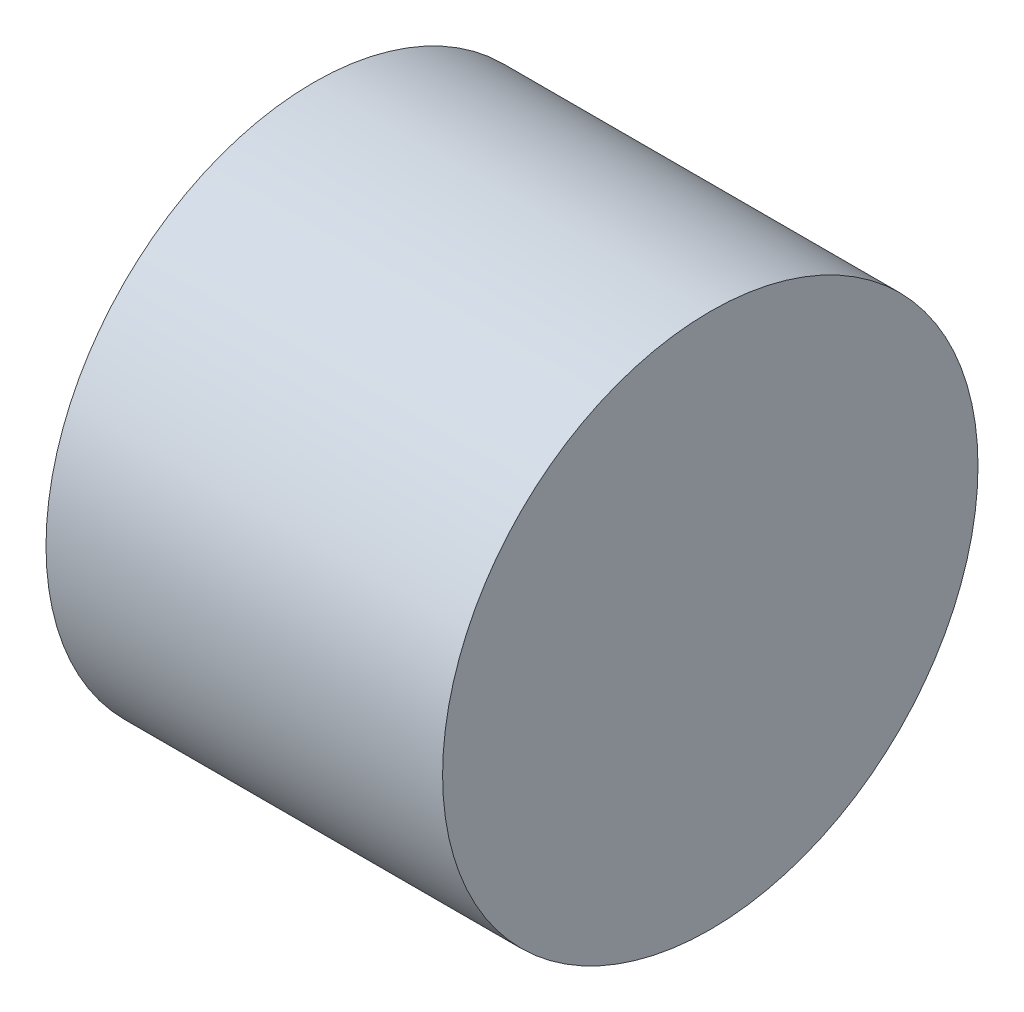
SolidWorks part; units mm, degrees
material "PVC Rigid"
ref_plane "Front Plane" through (0, 0, 0) normal (0, 0, 1) x (1, 0, 0)
ref_plane "Top Plane" through (0, 0, 0) normal (0, 1, 0) x (1, 0, 0)
ref_plane "Right Plane" through (0, 0, 0) normal (1, 0, 0) x (0, 0, -1)
sketch "Sketch1" plane through (0, 0, 0) normal (1, 0, 0) x (0, 0, -1)
  circle A0 centre (0, 0) radius 13.5
  dimension "D1" = 27
extrude "Boss-Extrude1" add sketch "Sketch1" along normal blind 20
